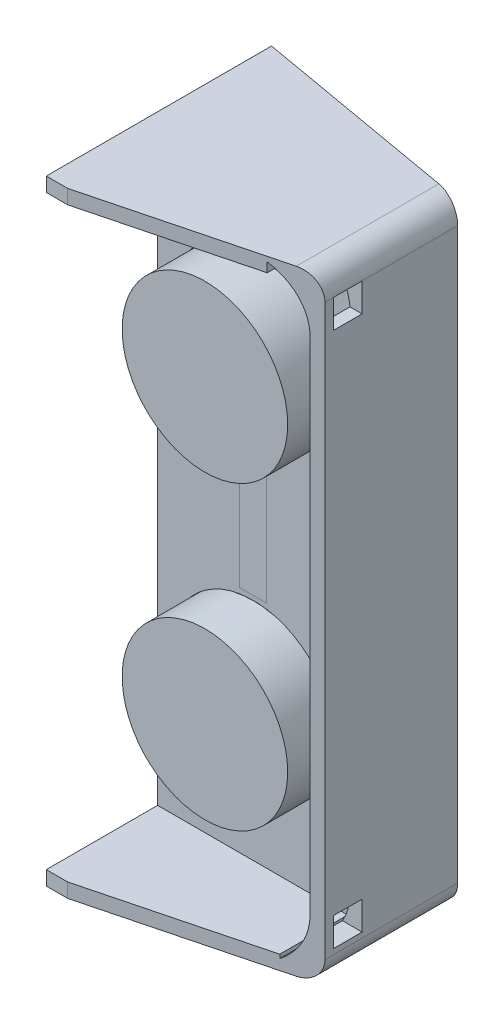
SolidWorks part; units mm, degrees
ref_plane "Front Plane" through (0, 0, 0) normal (0, 0, 1) x (1, 0, 0)
ref_plane "Top Plane" through (0, 0, 0) normal (0, 1, 0) x (1, 0, 0)
ref_plane "Right Plane" through (0, 0, 0) normal (1, 0, 0) x (0, 0, -1)
sketch "Sketch7" plane through (0, 0, 0) normal (0, 0, 1) x (1, 0, 0)
  line L68 (-111.2219, 0.1385) -> (111.0281, 0.1385) construction
  line L78 (117.3781, -142.6718) -> (187.2281, -142.6718) construction
  line L87 (111.0281, 124.6169) -> (111.0281, 92.8669) construction
  line L91 (111.0281, 124.6169) -> (111.0281, 92.8669) construction
  line L92 (117.3781, -142.6718) -> (187.2281, -142.6718) construction
  line L154 (123.7281, 130.9669) -> (187.2281, 130.9669) construction
  line L156 (123.7281, 130.9669) -> (187.2281, 130.9669) construction
  line L157 (-25.2083, 130.9669) -> (111.0281, 130.9669) construction
  line L158 (-25.2083, 130.9669) -> (111.0281, 130.9669) construction
  line L213 (117.3781, -136.3218) -> (117.3781, 124.6169)
  line L217 (117.3781, -136.3218) -> (117.3781, -142.6718)
  line L218 (117.3781, -142.6718) -> (187.2281, -142.6718)
  line L220 (212.6281, 105.5669) -> (212.6281, -117.2718)
  line L222 (187.2281, 130.9669) -> (117.3781, 130.9669)
  line L223 (117.3781, 130.9669) -> (117.3781, 124.6169)
  arc A43 (212.6281, -117.2718) -> (187.2281, -142.6718) centre (187.2281, -117.2718) cw
  arc A44 (212.6281, 105.5669) -> (187.2281, 130.9669) centre (187.2281, 105.5669) ccw
  circle A45 centre (159.9231, 61.1169) radius 36.83
  circle A46 centre (159.9231, -72.8218) radius 36.83
  circle A52 centre (198.5208, 117.0076) radius 1.905
  circle A53 centre (198.5208, -128.599) radius 1.905
  dimension "D1" = 69.85
  dimension "D4" = 25.4
  dimension "D9" = 73.66
  dimension "D3" = 38.1
extrude "Boss-Extrude1" add sketch "Sketch7" along normal blind 6.35
sketch "Sketch8" plane through (0, 0, 2.54) normal (0, 0, 1) x (1, 0, 0)
  circle A0 centre (160.02, 60.9785) radius 36.83
  circle A1 centre (160.02, -72.9602) radius 36.83
  dimension "D1" = 73.66
  dimension "D2" = 73.66
extrude "Boss-Extrude2" add sketch "Sketch8" along normal blind 25.4 and the other way blind 0.0003
sketch "Sketch9" plane through (0, 0, 0) normal (0, 0, -1) x (-1, 0, 0)
  circle A0 centre (-160.02, 60.9785) radius 34.925
  circle A1 centre (-160.02, -72.9602) radius 34.925
  dimension "D1" = 69.85
  dimension "D2" = 69.85
extrude "Cut-Extrude4" cut sketch "Sketch9" against normal blind 25.4
sketch "Sketch10" plane through (0, 0, 6.35) normal (0, 0, 1) x (1, 0, 0)
  line L0 (187.2281, 130.9669) -> (187.2281, 105.5669)
  line L1 (187.2281, 105.5669) -> (212.6281, 105.5669)
  line L2 (212.6281, -117.2718) -> (187.2281, -117.2718)
  line L3 (187.2281, -117.2718) -> (187.2281, -142.6718)
  arc A0 (212.6281, 105.5669) -> (187.2281, 130.9669) centre (187.2281, 105.5669) ccw construction
  arc A1 (187.2281, 130.9669) -> (212.6281, 105.5669) centre (187.2281, 105.5669) cw
  arc A2 (187.2281, -142.6718) -> (212.6281, -117.2718) centre (187.2281, -117.2718) ccw
extrude "Boss-Extrude3" add sketch "Sketch10" against normal blind 3.175
sketch "Sketch11" plane through (0, 0, 0) normal (0, 0, -1) x (-1, 0, 0)
  line L11 (-217.8922, -132.5118) -> (-217.8922, 120.8069)
  line L16 (-207.7322, 130.9669) -> (-187.2281, 130.9669)
  line L17 (-187.2281, -142.6718) -> (-207.7322, -142.6718)
  line L21 (-212.6281, 105.5669) -> (-212.6281, -117.2718)
  arc A2 (-187.2281, 130.9669) -> (-212.6281, 105.5669) centre (-187.2281, 105.5669) ccw
  arc A3 (-212.6281, -117.2718) -> (-187.2281, -142.6718) centre (-187.2281, -117.2718) ccw
  arc A4 (-217.8922, -132.5118) -> (-207.7322, -142.6718) centre (-207.7322, -132.5118) ccw
  arc A5 (-217.8922, 120.8069) -> (-207.7322, 130.9669) centre (-207.7322, 120.8069) cw
  dimension "D1" = 10.16
extrude "Boss-Extrude4" add sketch "Sketch11" along normal blind 38.1 and the other way blind 40.64
sketch "Sketch12" plane through (0, 0, 6.35) normal (0, 0, 1) x (1, 0, 0)
  line L15 (187.2281, 124.6169) -> (117.3781, 124.6169) construction
  line L18 (178.0511, 124.6169) -> (212.5469, 124.6169)
  line L23 (178.0511, 124.6169) -> (178.0511, -137.0862)
  line L27 (178.0511, -137.0862) -> (212.5469, -137.0862)
  line L29 (212.5469, 124.6169) -> (212.5469, -137.0862)
extrude "Cut-Extrude5" cut sketch "Sketch12" against normal blind 48.26 from offset 20.32 offset against normal yes
sketch "Sketch16" plane through (0, 130.9669, 0) normal (0, 1, 0) x (1, 0, 0)
  line L7 (217.8922, 26.67) -> (-101.0169, 82.7341)
  line L8 (217.8922, -40.64) -> (217.8922, 38.1) construction
  line L9 (-101.0169, 82.7341) -> (217.8922, 82.7341)
  line L10 (217.8922, 82.7341) -> (217.8922, 26.67)
  line L11 (217.8922, -32.3963) -> (47.5891, -76.3476)
  line L12 (217.8922, -40.64) -> (217.8922, 38.1) construction
  line L13 (47.5891, -76.3476) -> (217.8922, -67.4767)
  line L14 (217.8922, -67.4767) -> (217.8922, -32.3963)
  point P2 (131.9467, 41.3364)
  point P3 (128.3016, -58.1222)
  point P6 (42.6422, 57.4789)
  point P9 (47.5891, -76.3476)
  point P10 (217.8922, 82.7341)
sketch "Sketch18" plane through (0, 0, 0) normal (0, 0, -1) x (-1, 0, 0)
  line L0 (-187.2281, 130.9669) -> (-207.7322, 130.9669) construction
  line L1 (-207.7322, -142.6718) -> (-187.2281, -142.6718) construction
  line L2 (-197.4801, 130.9669) -> (-117.3781, 130.9669)
  line L3 (-197.4801, 130.9669) -> (-197.4801, 124.6169)
  line L4 (-197.4801, 124.6169) -> (-117.3781, 124.6169)
  line L5 (-117.3781, 130.9669) -> (-117.3781, 124.6169)
  line L7 (-117.3781, -136.3218) -> (-201.9067, -136.3218)
  line L8 (-117.3781, -136.3218) -> (-117.3781, -142.6718)
  line L9 (-117.3781, -142.6718) -> (-201.9067, -142.6718)
  line L10 (-201.9067, -136.3218) -> (-201.9067, -142.6718)
extrude "Boss-Extrude7" add sketch "Sketch18" along normal blind 66.04 and the other way blind 55.88
extrude "main angle" cut sketch "Sketch16" against normal through all
sketch "Sketch19" plane through (217.8922, 0, 0) normal (1, 0, 0) x (0, 0, -1)
  line L0 (-32.3963, 120.8069) -> (26.67, 120.8069) construction
  line L1 (-15.8658, -130.1366) -> (-28.5658, -130.1366)
  line L2 (-15.8658, -130.1366) -> (-15.8658, -117.4366)
  line L3 (-15.8658, -117.4366) -> (-28.5658, -117.4366)
  line L4 (-28.5658, -130.1366) -> (-28.5658, -117.4366)
  line L5 (-15.8658, 108.1069) -> (-28.5658, 108.1069)
  line L6 (-15.8658, 108.1069) -> (-15.8658, 120.8069)
  line L7 (-15.8658, 120.8069) -> (-28.5658, 120.8069)
  line L8 (-28.5658, 108.1069) -> (-28.5658, 120.8069)
  dimension "D1" = 12.7
  dimension "D2" = 12.7
  dimension "D3" = 12.7
  dimension "D4" = 12.7
extrude "Cut-Extrude8" cut sketch "Sketch19" against normal blind 45.72
sketch "Sketch20" plane through (0, 0, 0) normal (0, 0, -1) x (-1, 0, 0)
  line L1 (-169.0247, 25.4292) -> (-150.8215, 25.4292)
  line L2 (-169.0247, 25.4292) -> (-169.0247, -37.2974)
  line L3 (-169.0247, -37.2974) -> (-150.8215, -37.2974)
  line L4 (-150.8215, 25.4292) -> (-150.8215, -37.2974)
  circle A0 centre (-159.9231, 61.1169) radius 36.83 construction
  arc A1 (-129.8, -94.0125) -> (-190.1431, -51.7695) centre (-160.02, -72.9602) ccw construction
extrude "Cut-Extrude9" cut sketch "Sketch20" against normal blind 6.35 draft 26
sketch "Sketch23" plane through (0, 0, 0) normal (0, 0, -1) x (-1, 0, 0)
  circle A0 centre (-198.5208, 117.0076) radius 1.905
  circle A1 centre (-198.5208, -128.599) radius 1.905
extrude "Cut-Extrude10" cut sketch "Sketch23" against normal through all
sketch "Sketch24" plane through (0, 0, 2.5397) normal (0, 0, -1) x (-1, 0, 0)
  line L7 (-168.1761, 25.2235) -> (-151.98, 25.2235)
  line L8 (-168.1761, 25.2235) -> (-168.1761, -37.0185)
  line L9 (-168.1761, -37.0185) -> (-151.98, -37.0185)
  line L10 (-151.98, 25.2235) -> (-151.98, -37.0185)
  arc A0 (-190.1431, 82.1692) -> (-129.8, 39.9262) centre (-159.9231, 61.1169) ccw construction
  arc A1 (-129.8, -94.0125) -> (-190.1431, -51.7695) centre (-160.02, -72.9602) ccw construction
extrude "Boss-Extrude10" add sketch "Sketch24" against normal blind 3.81
